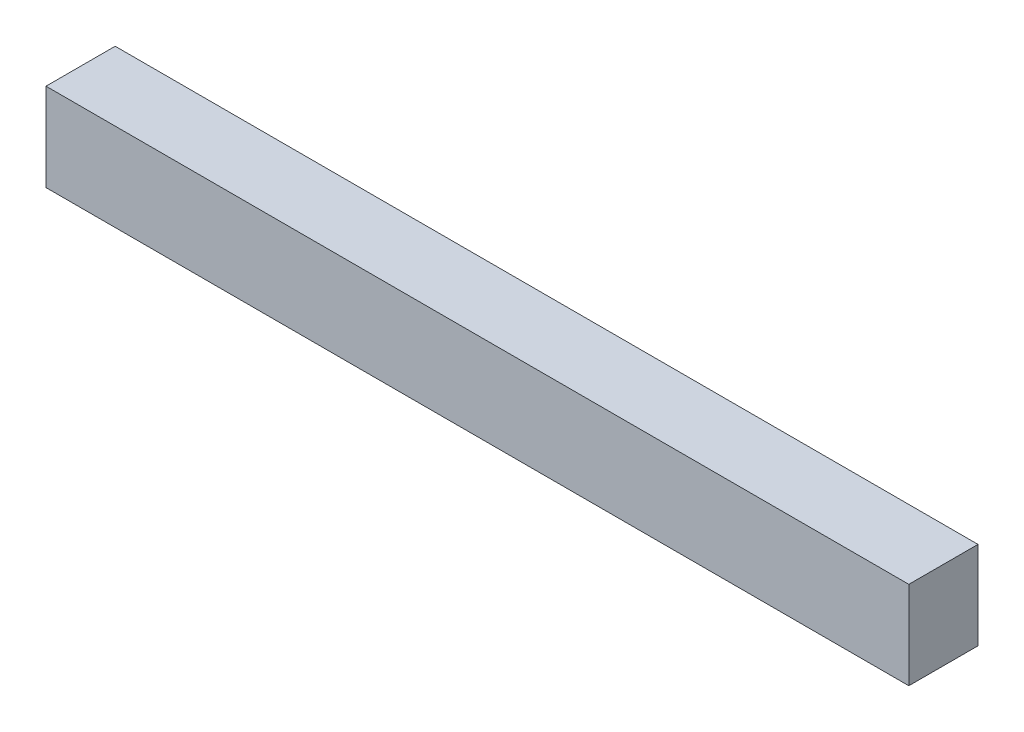
SolidWorks part; units mm, degrees
ref_plane "Front Plane" through (0, 0, 0) normal (0, 0, 1) x (1, 0, 0)
ref_plane "Top Plane" through (0, 0, 0) normal (0, 1, 0) x (1, 0, 0)
ref_plane "Right Plane" through (0, 0, 0) normal (1, 0, 0) x (0, 0, -1)
sketch "Sketch1" plane through (0, 0, 0) normal (0, 1, 0) x (1, 0, 0)
  line L1 (0, 0) -> (74.84, 0)
  line L2 (0, 0) -> (0, 6)
  line L3 (0, 6) -> (74.84, 6)
  line L4 (74.84, 0) -> (74.84, 6)
  dimension "D1" = 74.84
  dimension "D2" = 6
extrude "Boss-Extrude1" add sketch "Sketch1" along normal blind 7.62
